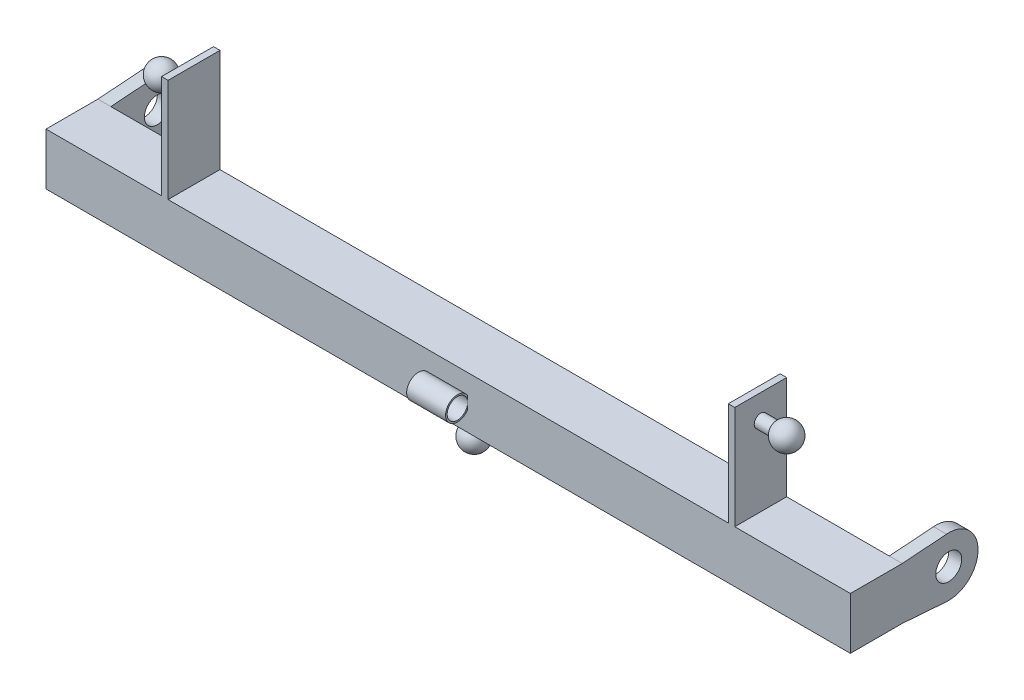
SolidWorks part; units mm, degrees
material "6061-T6 (SS)"
ref_plane "Front Plane" through (0, 0, 0) normal (0, 0, 1) x (1, 0, 0)
ref_plane "Top Plane" through (0, 0, 0) normal (0, 1, 0) x (1, 0, 0)
ref_plane "Right Plane" through (0, 0, 0) normal (1, 0, 0) x (0, 0, -1)
sketch "Sketch1" plane through (0, 0, 0) normal (1, 0, 0) x (0, 0, -1)
  line L0 (-23.8125, -23.8125) -> (-23.8125, 23.8125)
  line L1 (-25.4, -25.4) -> (25.4, -25.4)
  line L2 (-25.4, -25.4) -> (-25.4, 25.4)
  line L3 (-25.4, 25.4) -> (25.4, 25.4)
  line L4 (25.4, -25.4) -> (25.4, 25.4)
  line L5 (-25.4, -25.4) -> (25.4, 25.4) construction
  line L6 (-25.4, 25.4) -> (25.4, -25.4) construction
  line L7 (-23.8125, 23.8125) -> (23.8125, 23.8125)
  line L8 (23.8125, -23.8125) -> (23.8125, 23.8125)
  line L9 (-23.8125, -23.8125) -> (23.8125, -23.8125)
  point P0 (0, 0)
  dimension "D1" = 50.8
  dimension "D2" = 1.5875
extrude "Boss-Extrude1" add sketch "Sketch1" along normal mid plane 762
sketch "Sketch2" plane through (0, 0, 0) normal (1, 0, 0) x (0, 0, -1)
  circle A0 centre (-35.4106, 0) radius 10.0106
  circle A1 centre (-35.4106, 0) radius 11.5981
  dimension "D1" = 1.5875
extrude "Boss-Extrude2" add sketch "Sketch2" along normal mid plane 38.1
sketch "Sketch3" plane through (0, 25.4, 0) normal (0, 1, 0) x (1, 0, 0)
  line L0 (0, 0) -> (0, -64.2564) construction
  line L1 (381, -25.4) -> (-381, -25.4) construction
  line L2 (-280.543, -25.4) -> (-274.193, -25.4)
  line L3 (-280.543, -25.4) -> (-280.543, 25.4)
  line L4 (-280.543, 25.4) -> (-274.193, 25.4)
  line L5 (-274.193, -25.4) -> (-274.193, 25.4)
  line L6 (381, 25.4) -> (-381, 25.4) construction
  line L7 (274.193, -25.4) -> (274.193, 25.4)
  line L8 (280.543, 25.4) -> (274.193, 25.4)
  line L9 (280.543, -25.4) -> (280.543, 25.4)
  line L10 (280.543, -25.4) -> (274.193, -25.4)
  dimension "D1" = 6.35
  dimension "D2" = 274.193
extrude "Boss-Extrude3" add sketch "Sketch3" along normal blind 101.092
sketch "Sketch5" plane through (0, 0, 0) normal (0, 0, 1) x (1, 0, 0)
  line L0 (280.543, 102.616) -> (318.643, 102.616) construction
  line L1 (280.543, 126.492) -> (280.543, 25.4) construction
  line L2 (280.543, 108.966) -> (294.9445, 108.966)
  line L3 (280.543, 108.966) -> (280.543, 102.616)
  line L4 (280.543, 102.616) -> (318.643, 102.616)
  arc A0 (318.643, 102.616) -> (294.9445, 108.966) centre (305.943, 102.616) ccw
  point P8 (0, 0)
  point P9 (0, 0)
  dimension "D2" = 25.4
  dimension "D1" = 77.216
  dimension "D3" = 25.4
  dimension "D4" = 6.35
revolve "Revolve1" add sketch "Sketch5" angle 360 about L0
mirror "Mirror1" about plane through (0, 0, 0) normal (1, 0, 0) of "Revolve1"
sketch "Sketch6" plane through (0, 0, 0) normal (1, 0, 0) x (0, 0, -1)
  line L0 (0, -25.4) -> (0, -75.0825) construction
  line L1 (-25.4, -25.4) -> (25.4, -25.4) construction
  line L2 (-6.35, -25.4) -> (0, -25.4)
  line L3 (0, -25.4) -> (0, -63.5)
  line L4 (-6.35, -25.4) -> (-6.35, -39.8015)
  arc A0 (-6.35, -39.8015) -> (0, -63.5) centre (0, -50.8) ccw
  dimension "D1" = 25.4
  dimension "D2" = 25.4
  dimension "D3" = 6.35
revolve "Revolve2" add sketch "Sketch6" angle 360 about L0
sketch "Sketch7" plane through (381, 0, 0) normal (1, 0, 0) x (0, 0, -1)
  line L0 (68.7131, -28.6524) -> (25.4, -25.4)
  line L1 (25.4, -25.4) -> (-25.4, -25.4)
  line L2 (-25.4, -25.4) -> (-25.4, 25.4)
  line L3 (-25.4, 25.4) -> (25.4, 25.4)
  line L4 (25.4, 25.4) -> (68.7131, 28.6524)
  arc A0 (68.7131, -28.6524) -> (68.7131, 28.6524) centre (70.8646, 0) ccw
  circle A1 centre (70.8646, 0) radius 12.7
  dimension "D1" = 25.4
extrude "Boss-Extrude4" add sketch "Sketch7" along normal blind 12.7
mirror "Mirror2" about plane through (0, 0, 0) normal (1, 0, 0) of "Boss-Extrude4"
